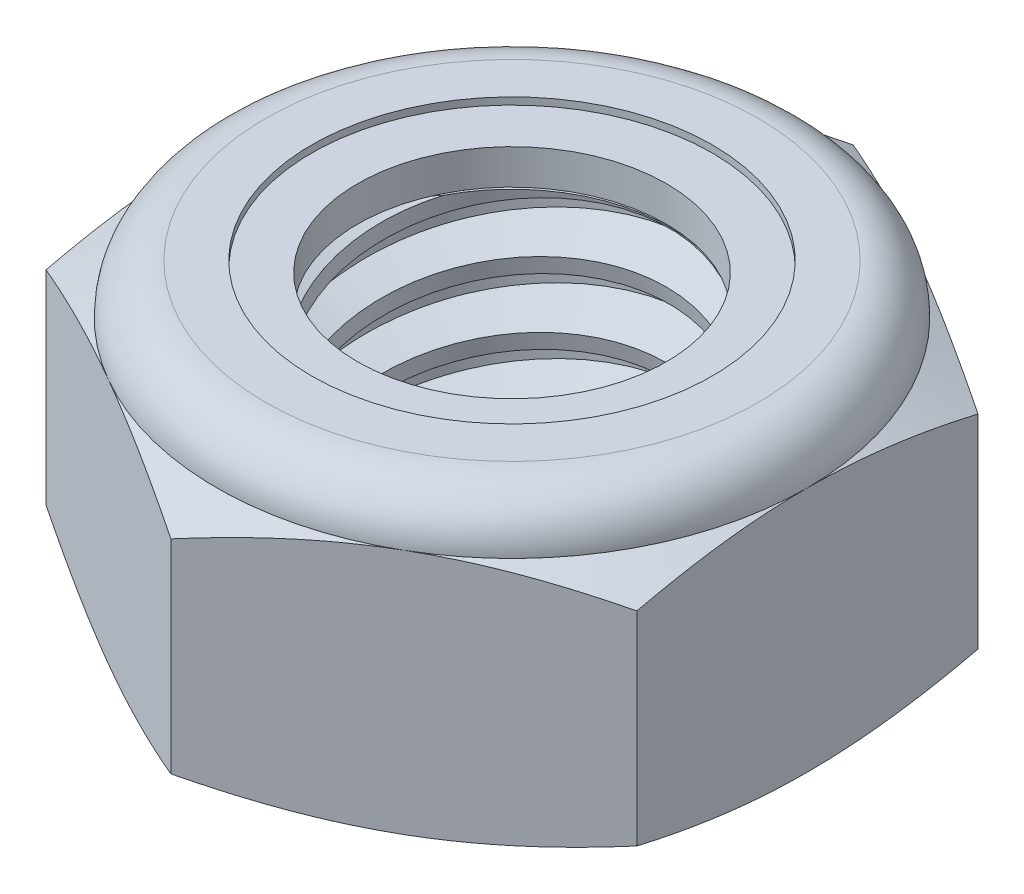
SolidWorks part; units mm, degrees
material "AISI 316 Annealed Stainless Steel Bar (SS)"
ref_plane "Front" through (0, 0, 0) normal (0, 0, 1) x (1, 0, 0)
ref_plane "Top" through (0, 0, 0) normal (0, 1, 0) x (1, 0, 0)
ref_plane "Right" through (0, 0, 0) normal (1, 0, 0) x (0, 0, -1)
sketch "Sketch1" plane through (0, 0, 0) normal (0, 1, 0) x (1, 0, 0)
  line L1 (0, 7.3323) -> (-6.35, 3.6662)
  line L2 (-6.35, 3.6662) -> (-6.35, -3.6662)
  line L3 (-6.35, -3.6662) -> (0, -7.3323)
  line L4 (0, -7.3323) -> (6.35, -3.6662)
  line L5 (6.35, -3.6662) -> (6.35, 3.6662)
  line L6 (6.35, 3.6662) -> (0, 7.3323)
  circle A0 centre (0, 0) radius 6.35 construction
  dimension "Hex Flats" = 12.7
extrude "Extrude1" add sketch "Sketch1" along normal blind 6.35
sketch "Sketch2" plane through (0, 0, 0) normal (1, 0, 0) x (0, 0, -1)
  line L0 (-3.9624, 0) -> (-3.9624, 6.35) construction
  line L1 (0, 0) -> (3.9624, 0)
  line L2 (0, 0) -> (0, 6.35)
  line L3 (0, 6.35) -> (3.9624, 6.35)
  line L4 (3.9624, 0) -> (3.9624, 6.35)
  line L5 (-3.6662, 6.35) -> (3.6662, 6.35) construction
  line L7 (0, -3.9624) -> (0, 0) construction
  dimension "Thread Dia" = 7.9248
revolve "Revolve1" add sketch "Sketch2" angle 360 about L7
sketch "Sketch3" plane through (0, 0, 0) normal (1, 0, 0) x (0, 0, -1)
  line L0 (3.9624, 6.35) -> (-3.9624, 6.35) construction
  line L1 (-3.9624, 6.35) -> (-3.9624, 4.9389) construction
  line L2 (-3.9624, 4.9389) -> (3.9624, 6.35) construction
  line L3 (3.9624, 6.35) -> (3.9933, 6.1763) construction
  line L4 (3.9933, 6.1763) -> (4.2098, 4.9607)
  line L5 (4.2098, 4.9607) -> (3.3805, 5.261)
  line L6 (3.3805, 5.261) -> (3.3187, 5.6083)
  line L7 (3.3187, 5.6083) -> (3.9933, 6.1763)
  line L8 (3.3496, 5.4346) -> (4.1015, 5.5685) construction
  line L9 (3.9624, 6.35) -> (3.9624, 5.5438) construction
  line L10 (3.9624, 5.5438) -> (-3.9624, 4.1327) construction
  line L11 (-3.9624, 4.1327) -> (-3.9624, 4.9389) construction
  line L12 (-0.2692, 6.35) -> (0.2692, 3.3264) construction
  line L13 (-3.9624, 0) -> (-3.9624, 6.35) construction
  line L14 (0, 6.35) -> (3.9624, 6.35) construction
  line L15 (3.9624, 0) -> (3.9624, 6.35) construction
  point P13 (0, 4.8382)
  dimension "D1" = 0.1764
  dimension "D2" = 0.3528
  dimension "Thread Pitch" = 1.4111
  dimension "D4" = 60
  dimension "D5" = 1.4111
revolve "Cut-Revolve1" cut sketch "Sketch3" angle 360 about L12
pattern_linear "LPattern1" count 5 spacing 1.4111 along (0, 1, 0) count 2 spacing 1.4111 along (0, 1, 0) of "Cut-Revolve1"
sketch "Sketch4" plane through (0, 0, 0) normal (1, 0, 0) x (0, 0, -1)
  line L0 (0, 6.35) -> (3.9624, 6.35)
  line L1 (3.9624, 6.35) -> (3.3187, 6.0498)
  line L2 (3.3187, 6.0498) -> (3.3187, 0.3002)
  line L3 (3.3187, 0.3002) -> (3.9624, 0)
  line L4 (3.9624, 0) -> (0, 0)
  line L5 (0, 0) -> (0, 6.35)
  line L6 (3.9624, 0) -> (3.9624, 6.35) construction
  line L7 (0, 6.35) -> (3.9624, 6.35) construction
  line L8 (0, 0) -> (3.9624, 0) construction
  line L9 (0, 0) -> (0, 6.35) construction
  line L10 (0, 6.35) -> (0, 7.0603) construction
  dimension "D1" = 25
revolve "Cut-Revolve2" cut sketch "Sketch4" angle 360 about L10
combine bodies "Combine1" operation type subtract main body 112 bodies to subtract 111
sketch "Sketch5" plane through (0, 0, 0) normal (1, 0, 0) x (0, 0, -1)
  line L0 (0, 0) -> (6.35, 0)
  line L1 (6.35, 0) -> (7.3323, 0.4581)
  line L2 (7.3323, 0.4581) -> (7.3323, 4.8336)
  line L3 (7.3323, 4.8336) -> (6.35, 5.2917)
  line L4 (5.2917, 6.35) -> (5.2917, 7.62)
  line L5 (5.2917, 7.62) -> (8.6023, 7.62)
  line L6 (8.6023, 7.62) -> (8.6023, -1.27)
  line L7 (8.6023, -1.27) -> (0, -1.27)
  line L8 (0, -1.27) -> (0, 0)
  line L9 (6.35, 5.2917) -> (6.35, 0) construction
  line L10 (0, 0) -> (3.9624, 0) construction
  line L13 (7.3323, 2.6458) -> (8.6023, 2.6458) construction
  line L14 (7.3323, 6.35) -> (7.3323, 0) construction
  line L15 (0, 0) -> (0, 7.62) construction
  line L20 (0, 7.62) -> (5.2917, 7.62) construction
  line L22 (0, 6.35) -> (3.9624, 6.35) construction
  arc A0 (6.35, 5.2917) -> (5.2917, 6.35) centre (5.2917, 5.2917) ccw
  dimension "D1" = 25
  dimension "D2" = 1.27
  dimension "D3" = 6.35
  dimension "D4" = 1.0583
revolve "Cut-Revolve3" cut sketch "Sketch5" angle 360 about L15
sketch "Sketch6" plane through (0, 0, 0) normal (1, 0, 0) x (0, 0, -1)
  line L0 (0, 5.2917) -> (6.1976, 5.2917)
  line L1 (5.2917, 6.1976) -> (4.3052, 6.1976)
  line L2 (0, 7.62) -> (0, 5.2917)
  line L3 (4.3052, 7.62) -> (0, 7.62)
  line L4 (0, 7.62) -> (5.2917, 7.62) construction
  line L5 (0, 0) -> (0, 7.62) construction
  line L6 (0, 7.62) -> (0, 44.323) construction
  line L7 (4.3052, 6.1976) -> (4.3052, 7.62)
  line L8 (5.2917, 6.35) -> (5.2917, 6.1976) construction
  line L9 (4.3052, 6.1976) -> (3.3187, 6.1976) construction
  line L10 (3.3187, 6.1976) -> (3.3187, 6.0498) construction
  arc A0 (6.1976, 5.2917) -> (5.2917, 6.1976) centre (5.2917, 5.2917) ccw
  arc A1 (6.35, 5.2917) -> (5.2917, 6.35) centre (5.2917, 5.2917) ccw construction
  dimension "D1" = 0.1524
revolve "Cut-Revolve4" cut sketch "Sketch6" angle 360 about L6
sketch "Sketch7" plane through (0, 0, 0) normal (1, 0, 0) x (0, 0, -1)
  line L0 (3.3187, 5.3679) -> (6.1179, 5.3679)
  line L1 (5.2917, 6.1214) -> (3.3187, 6.1214)
  line L2 (3.3187, 6.1214) -> (3.3187, 5.3679)
  line L3 (3.3187, 5.3679) -> (0, 5.3679) construction
  line L4 (0, 5.3679) -> (0, 6.1214) construction
  line L5 (0, 6.1214) -> (3.3187, 6.1214) construction
  line L6 (3.3187, 5.3679) -> (3.3187, 5.2917) construction
  line L7 (0, 5.2917) -> (6.1976, 5.2917) construction
  line L8 (5.2917, 6.1214) -> (5.2917, 6.1976) construction
  arc A0 (6.1179, 5.3679) -> (5.2917, 6.1214) centre (5.2917, 5.2917) ccw
  arc A2 (6.1976, 5.2917) -> (5.2917, 6.1976) centre (5.2917, 5.2917) ccw construction
  dimension "D1" = 0.0762
revolve "Revolve2" add sketch "Sketch7" angle 360 about L4
equation "\"D1@Sketch3\"=\"Thread Pitch@Sketch3\"/8"
equation "\"D2@Sketch3\"=\"Thread Pitch@Sketch3\"/4"
equation "\"D5@Sketch3\"=\"Thread Pitch@Sketch3\""
equation "\"D4@LPattern1\"=\"Thread Pitch@Sketch3\""
equation "\"D3@LPattern1\"=\"Thread Pitch@Sketch3\""
equation "\"D1@LPattern1\"=\"Height@Extrude1\"/\"Thread Pitch@Sketch3\""
equation "\"D4@Sketch5\"=\"Height@Extrude1\"/6"
